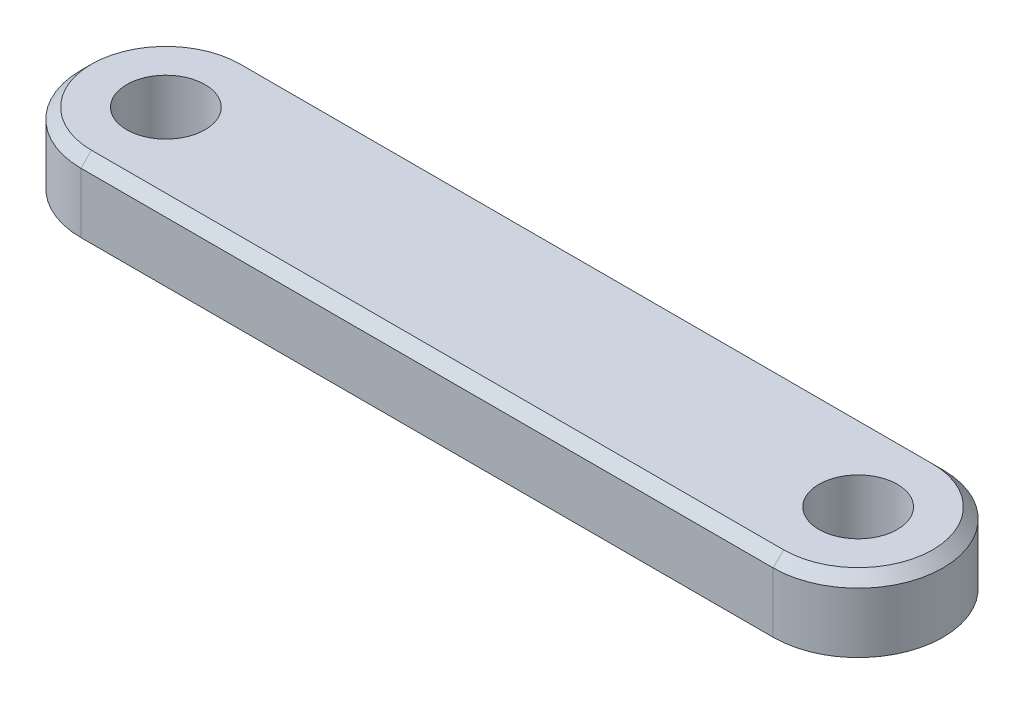
SolidWorks part; units mm, degrees
ref_plane "Front Plane" through (0, 0, 0) normal (0, 0, 1) x (1, 0, 0)
ref_plane "Top Plane" through (0, 0, 0) normal (0, 1, 0) x (1, 0, 0)
ref_plane "Right Plane" through (0, 0, 0) normal (1, 0, 0) x (0, 0, -1)
sketch "Sketch1" plane through (0, 0, 0) normal (0, 1, 0) x (1, 0, 0)
  line L0 (-18.0944, 0) -> (24.4801, 0) construction
  line L1 (-13.25, 0) -> (13.25, 0) construction
  line L2 (-13.25, 3.25) -> (13.25, 3.25)
  line L3 (-13.25, -3.25) -> (13.25, -3.25)
  line L4 (0, 10.1131) -> (0, -14.786) construction
  arc A0 (-13.25, 3.25) -> (-13.25, -3.25) centre (-13.25, 0) ccw
  arc A1 (13.25, -3.25) -> (13.25, 3.25) centre (13.25, 0) ccw
  circle A2 centre (-13.25, 0) radius 1.5
  circle A4 centre (13.25, 0) radius 1.5
  point P5 (0, 0)
  point P11 (-16.5, 0)
  point P12 (16.5, 0)
  dimension "D3" = 3
  dimension "D1" = 6.5
  dimension "D2" = 33
extrude "Boss-Extrude1" add sketch "Sketch1" along normal mid plane 2.7
chamfer "Chamfer1" distance 0.4 angle 45 4 edges at (16.5, 1.35, 0) (0, 1.35, -3.25) (-16.5, 1.35, 0) (0, 1.35, 3.25)
